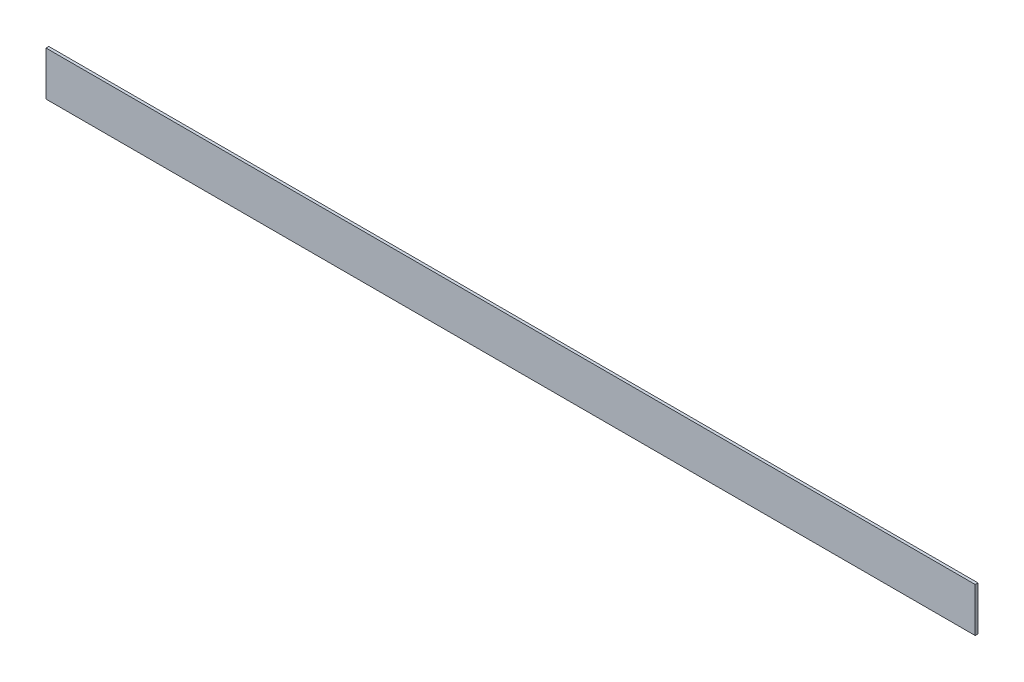
SolidWorks part; units mm, degrees
material "Nylon 6/10"
ref_plane "Front Plane" through (0, 0, 0) normal (0, 0, 1) x (1, 0, 0)
ref_plane "Top Plane" through (0, 0, 0) normal (0, 1, 0) x (1, 0, 0)
ref_plane "Right Plane" through (0, 0, 0) normal (1, 0, 0) x (0, 0, -1)
sketch "Sketch1" plane through (0, 0, 0) normal (0, 0, 1) x (1, 0, 0)
  line L6 (0, 0) -> (-1066.8, 0)
  line L7 (0, 0) -> (0, -50.8)
  line L8 (0, -50.8) -> (-1066.8, -50.8)
  line L9 (-1066.8, 0) -> (-1066.8, -50.8)
  dimension "D1" = 50.8
  dimension "D2" = 1066.8
extrude "Boss-Extrude1" add sketch "Sketch1" along normal blind 3.175
